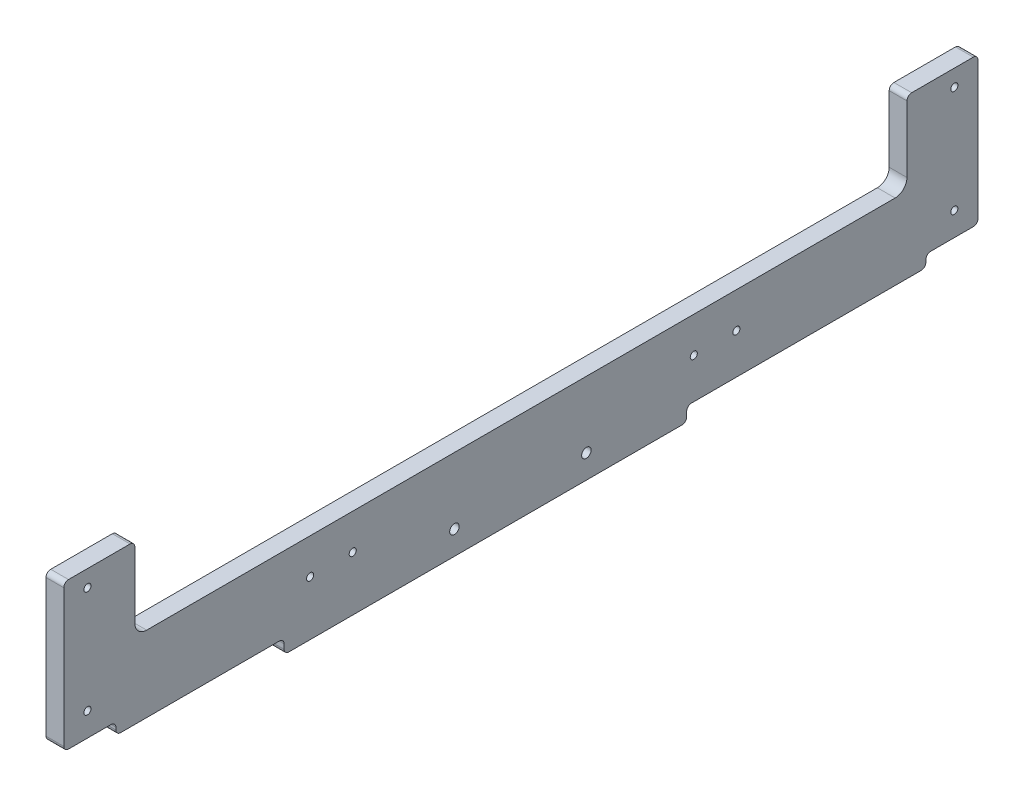
SolidWorks part; units mm, degrees
ref_plane "Front" through (0, 0, 0) normal (0, 0, 1) x (1, 0, 0)
ref_plane "Top" through (0, 0, 0) normal (0, 1, 0) x (1, 0, 0)
ref_plane "Right" through (0, 0, 0) normal (1, 0, 0) x (0, 0, -1)
sketch "草图1" plane through (0, 0, 0) normal (1, 0, 0) x (0, 0, -1)
  line L0 (0, 32) -> (0, 0)
  line L1 (0, 0) -> (15, 0)
  line L2 (15, 0) -> (15, -6)
  line L3 (15, -6) -> (185, -6)
  line L4 (185, -6) -> (185, 0)
  line L5 (185, 0) -> (205, 0)
  line L6 (205, 0) -> (205, 32)
  line L7 (205, 32) -> (0, 32)
  dimension "D1" = 15
  dimension "D2" = 6
  dimension "D3" = 170
  dimension "D4" = 20
  dimension "D5" = 38
extrude "凸台-拉伸1" add sketch "草图1" along normal blind 7.5
sketch "草图2" plane through (7.5, 0, 0) normal (1, 0, 0) x (0, 0, -1)
  line L0 (102.5, -6) -> (102.5, 32) construction
  line L1 (15, -6) -> (185, -6) construction
  line L2 (205, 32) -> (0, 32) construction
  circle A0 centre (86.95, 4) radius 2
  circle A1 centre (142.65, 4) radius 2
  dimension "D1" = 4
  dimension "D2" = 4
  dimension "D3" = 55.7
  dimension "D4" = 10
extrude "切除-拉伸1" cut sketch "草图2" against normal through all
sketch "草图3" plane through (7.5, 0, 0) normal (1, 0, 0) x (0, 0, -1)
  line L0 (102.5, 32) -> (102.5, -6) construction
  line L1 (205, 32) -> (0, 32) construction
  circle A0 centre (64.8, 24) radius 1.75
  circle A1 centre (164.8, 24) radius 1.75
  dimension "D1" = 3.5
  dimension "D2" = 3.5
  dimension "D3" = 100
  dimension "D4" = 8
extrude "切除-拉伸2" [suppressed] cut sketch "草图3" against normal up to next
sketch "草图4" plane through (7.5, 0, 0) normal (1, 0, 0) x (0, 0, -1)
  line L0 (0, 18) -> (-8, 18)
  line L1 (0, 32) -> (0, 0) construction
  line L2 (-8, 18) -> (-8, -2)
  line L3 (-8, -2) -> (0, -2)
  line L4 (0, -2) -> (0, 18)
  line L5 (205, 32) -> (0, 32) construction
  line L6 (0, 18) -> (0, -2)
  line L7 (205, 18) -> (213, 18)
  line L8 (205, 0) -> (205, 32) construction
  line L9 (213, 18) -> (213, -2)
  line L10 (213, -2) -> (205, -2)
  line L11 (205, -2) -> (205, 18)
  line M7 (0, 32) -> (0, 0)
  line M13 (205, 0) -> (205, 32)
  dimension "D1" = 8
  dimension "D2" = 20
  dimension "D3" = 34
  dimension "D4" = 8
  dimension "D5" = 20
extrude "凸台-拉伸2" [suppressed] add sketch "草图4" against normal up to surface (7.5 mm away) contours L10 L9 L7 M13 | L2 L3 L0 M7
sketch "草图5" plane through (7.5, 0, 0) normal (1, 0, 0) x (0, 0, -1)
  circle A0 centre (5.3, 34) radius 1.25
  circle A1 centre (222.56, 34) radius 1.25
  dimension "D1" = 2.5
  dimension "D2" = 2.5
extrude "切除-拉伸3" [suppressed] cut sketch "草图5" against normal through all
sketch "草图6" plane through (7.5, 0, 0) normal (1, 0, 0) x (0, 0, -1)
  line L0 (205, 32) -> (0, 32) construction
  line L1 (0, 32) -> (0, 0) construction
  line L5 (55.6098, -22) -> (145.6098, -22)
  line L6 (55.6098, -22) -> (55.6098, 2)
  line L7 (55.6098, 2) -> (145.6098, 2)
  line L8 (145.6098, -22) -> (145.6098, 2)
  line L9 (55.6098, -22) -> (145.6098, 2) construction
  line L10 (55.6098, 2) -> (145.6098, -22) construction
  circle A0 centre (25, -3) radius 12.5
  circle A1 centre (179.3892, 54) radius 12.5
  point P10 (100.6098, -10)
  dimension "D1" = 25
  dimension "D2" = 35
  dimension "D3" = 25
  dimension "D4" = 42
  dimension "D5" = 24
  dimension "D6" = 90
extrude "切除-拉伸4" [suppressed] cut sketch "草图6" against normal up to next
fillet "圆角2" [suppressed] radius 6
sketch "草图7" plane through (7.5, 0, 0) normal (1, 0, 0) x (0, 0, -1)
  circle A0 centre (93.433, 66.8186) radius 5
  circle A1 centre (119.9148, 66.8186) radius 5
  circle A2 centre (146.7178, 66.8186) radius 5
  circle A3 centre (69.7794, 66.8186) radius 5
  circle A4 centre (24.4255, 16.3066) radius 5
  circle A5 centre (16.5587, 66.8186) radius 5
  circle A8 centre (174.2698, 16.3066) radius 5
  circle A9 centre (51.4941, 16.3066) radius 5
  circle A10 centre (112.882, 16.3066) radius 5
  dimension "D1" = 10
  dimension "D2" = 10
  dimension "D3" = 10
  dimension "D4" = 10
  dimension "D5" = 10
  dimension "D6" = 10
  dimension "D9" = 10
  dimension "D10" = 10
  dimension "D11" = 10
extrude "切除-拉伸5" [suppressed] cut sketch "草图7" against normal up to next
sketch "草图9" plane through (7.5, 0, 0) normal (1, 0, 0) x (0, 0, -1)
  line L0 (205, 32) -> (0, 32) construction
  line L1 (0, 0) -> (-78, 0)
  line L2 (0, 0) -> (0, 32)
  line L3 (0, 32) -> (-78, 32)
  line L4 (-78, 0) -> (-78, 32)
  line L5 (205, 0) -> (308, 0)
  line L6 (205, 0) -> (205, 32)
  line L7 (205, 32) -> (308, 32)
  line L8 (308, 0) -> (308, 32)
  dimension "D1" = 78
  dimension "D2" = 103
extrude "凸台-拉伸3" add sketch "草图9" against normal up to surface (7.5 mm away) up to face at (0, 4, -144.65)
sketch "草图11" plane through (7.5, 0, 0) normal (1, 0, 0) x (0, 0, -1)
  line L1 (-78, 32) -> (-48, 32)
  line L2 (-78, 32) -> (-78, 67)
  line L3 (-78, 67) -> (-48, 67)
  line L4 (-48, 32) -> (-48, 67)
  line L5 (308, 32) -> (278, 32)
  line L6 (308, 32) -> (308, 67)
  line L7 (308, 67) -> (278, 67)
  line L8 (278, 32) -> (278, 67)
  dimension "D1" = 35
  dimension "D2" = 30
  dimension "D3" = 35
  dimension "D4" = 30
extrude "凸台-拉伸4" add sketch "草图11" against normal up to surface (7.5 mm away) up to face at (0, 4, -144.65)
sketch "草图10" plane through (7.5, 0, 0) normal (1, 0, 0) x (0, 0, -1)
  line L0 (-78, 0) -> (15, 0) construction
  line L1 (-78, 67) -> (-78, 0) construction
  line L2 (308, 0) -> (308, 67) construction
  line L3 (185, 0) -> (308, 0) construction
  circle A0 centre (-68, 15) radius 1.5
  circle A1 centre (298, 15) radius 1.5
  circle A2 centre (-68, 60) radius 1.5
  circle A3 centre (298, 60) radius 1.5
  dimension "D1" = 3
  dimension "D2" = 3
  dimension "D5" = 3
  dimension "D9" = 3
  dimension "D3" = 15
  dimension "D4" = 10
  dimension "D6" = 45
  dimension "D7" = 10
  dimension "D8" = 15
  dimension "D10" = 45
extrude "切除-拉伸6" cut sketch "草图10" against normal through all
fillet "圆角1" radius 2 10 edges at (3.75, -6, -15) (3.75, -6, -185) (3.75, 0, -308) (3.75, 0, -185) (3.75, 0, -15) (3.75, 0, 78) (3.75, 67, -278) (3.75, 67, -308) (3.75, 67, 48) (3.75, 67, 78)
fillet "圆角3" radius 5 2 edges at (3.75, 32, -278) (3.75, 32, 48)
sketch "草图12" plane through (7.5, 0, 0) normal (1, 0, 0) x (0, 0, -1)
  line L0 (-78, 65) -> (-78, 2) construction
  line L1 (-78, 5) -> (-56, 5)
  line L2 (-78, 5) -> (-78, 0)
  line L3 (-78, 0) -> (-56, 0)
  line L4 (-56, 5) -> (-56, 0)
  line L5 (-76, 0) -> (13, 0) construction
  line L6 (187, 0) -> (306, 0) construction
  line L7 (308, 0) -> (286, 0)
  line L8 (308, 0) -> (308, 5)
  line L9 (308, 5) -> (286, 5)
  line L10 (286, 0) -> (286, 5)
  line L11 (308, 2) -> (308, 65) construction
  dimension "D1" = 22
  dimension "D2" = 5
  dimension "D3" = 22
  dimension "D4" = 5
extrude "切除-拉伸7" cut sketch "草图12" against normal through all
fillet "圆角4" radius 2 6 edges at (3.75, 5, 78) (3.75, 5, 56) (3.75, 0, 56) (3.75, 5, -286) (3.75, 0, -286) (3.75, 5, -308)
sketch "草图13" plane through (7.5, 0, 0) normal (1, 0, 0) x (0, 0, -1)
  circle A0 centre (206, 17) radius 1.5
  circle A1 centre (188, 17) radius 1.5
  circle A2 centre (44, 17) radius 1.5
  circle A3 centre (26, 17) radius 1.5
  dimension "D1" = 3
  dimension "D2" = 3
  dimension "D3" = 3
  dimension "D4" = 3
extrude "切除-拉伸8" cut sketch "草图13" against normal through all
